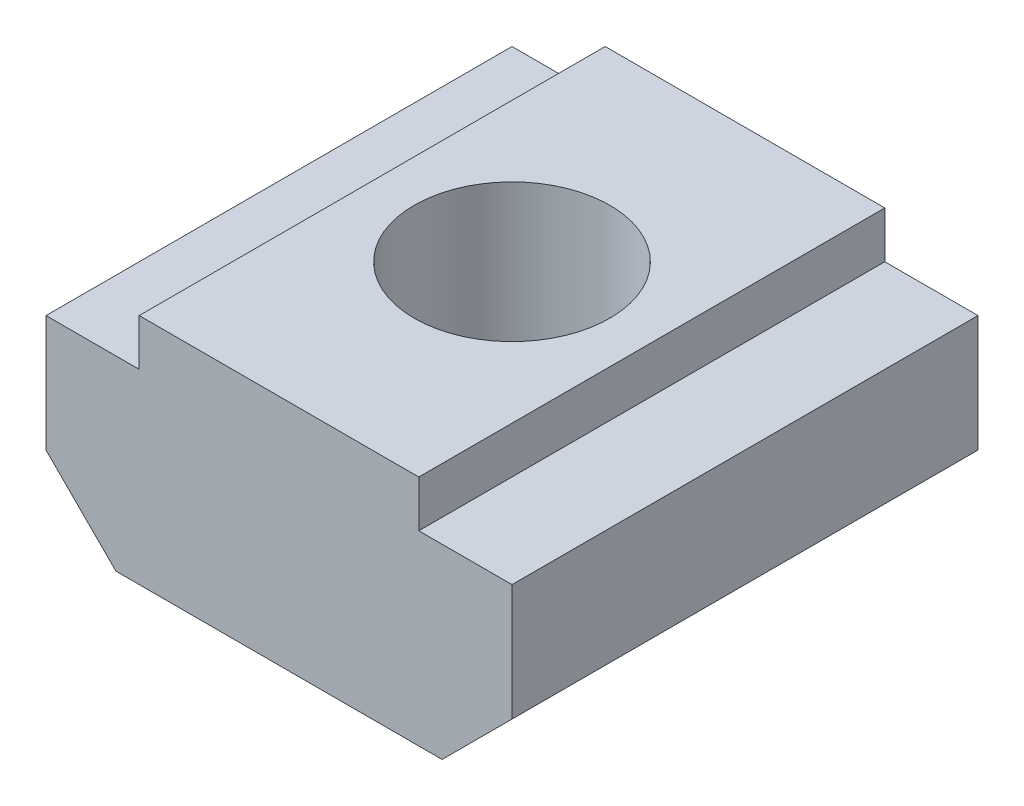
SolidWorks part; units mm, degrees
ref_plane "Front Plane" through (0, 0, 0) normal (0, 0, 1) x (1, 0, 0)
ref_plane "Top Plane" through (0, 0, 0) normal (0, 1, 0) x (1, 0, 0)
ref_plane "Right Plane" through (0, 0, 0) normal (1, 0, 0) x (0, 0, -1)
sketch "Sketch1" plane through (0, 0, 0) normal (0, 0, 1) x (1, 0, 0)
  line L0 (-5, -1) -> (-3.5, -2.5)
  line L1 (-3, -2.5) -> (3, -2.5)
  line L2 (-3, -2.5) -> (-3, 2.5)
  line L3 (-3, 2.5) -> (3, 2.5)
  line L4 (3, -2.5) -> (3, 2.5)
  line L5 (-3, -2.5) -> (3, 2.5) construction
  line L6 (-3, 2.5) -> (3, -2.5) construction
  line L7 (-5, -2.5) -> (5, -2.5)
  line L8 (-5, -2.5) -> (-5, 1.5)
  line L9 (-5, 1.5) -> (5, 1.5)
  line L10 (5, -2.5) -> (5, 1.5)
  line L11 (5, -1) -> (3.5, -2.5)
  line L12 (-5, -1) -> (5, -1) construction
  line L13 (0, -1) -> (0, 0) construction
  point P0 (0, 0)
  dimension "D1" = 6
  dimension "D2" = 5
  dimension "D3" = 10
  dimension "D4" = 4
  dimension "D5" = 7
  dimension "D6" = 45
extrude "Boss-Extrude1" add sketch "Sketch1" along normal mid plane 10 contours L9 L8 L0 L7 L2 | L9 L2 L1 L4 | L2 L9 L4 L3 | L11 L10 L9 L4 L7
sketch "Sketch2" plane through (0, 2.5, 0) normal (0, 1, 0) x (1, 0, 0)
  circle A0 centre (0, 0) radius 2.1
  dimension "D1" = 4.2
extrude "Cut-Extrude1" cut sketch "Sketch2" against normal through all
